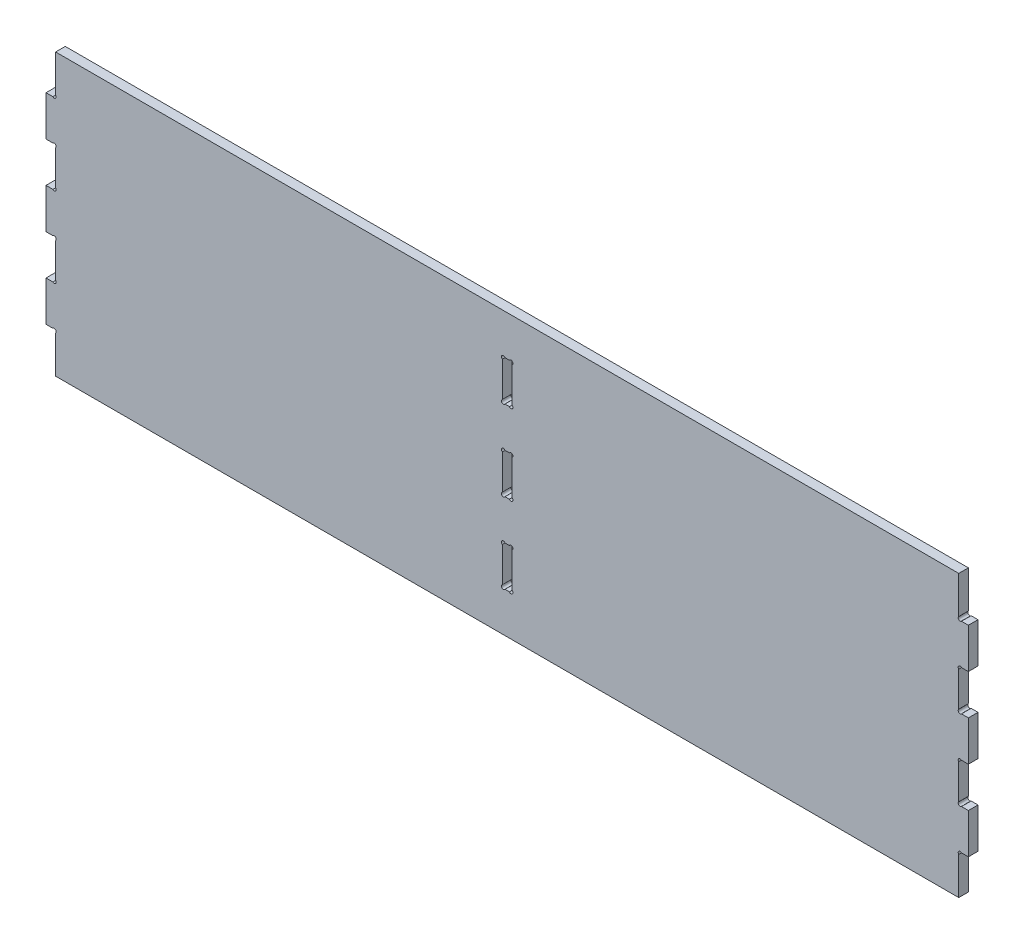
SolidWorks part; units mm, degrees
ref_plane "Front Plane" through (0, 0, 0) normal (0, 0, 1) x (1, 0, 0)
ref_plane "Top Plane" through (0, 0, 0) normal (0, 1, 0) x (1, 0, 0)
ref_plane "Right Plane" through (0, 0, 0) normal (1, 0, 0) x (0, 0, -1)
sketch "Sketch1" plane through (0, 0, 0) normal (0, 0, 1) x (1, 0, 0)
  line L0 (511.8067, 188.9039) -> (511.8067, 142.2993)
  line L1 (-613.9221, 188.9039) -> (511.8067, 188.9039)
  line L2 (-625.9221, -111.0961) -> (-625.9221, -61.0961)
  line L3 (-613.9221, -161.0961) -> (511.8067, -161.0961)
  line L4 (523.8067, 138.3198) -> (523.8067, 88.9039)
  line L5 (512.303, 138.9063) -> (512.303, 88.9039) construction
  line L6 (518.8067, 88.9039) -> (515.202, 88.9039)
  line L7 (511.8067, 85.5109) -> (511.8067, 42.2969)
  line L8 (515.202, 38.9039) -> (518.8067, 38.9039)
  line L9 (523.8067, 38.9039) -> (523.8067, -11.0961)
  line L10 (518.8067, -11.0961) -> (515.202, -11.0961)
  line L11 (511.8067, -14.4891) -> (511.8067, -57.7031)
  line L12 (515.202, -61.0961) -> (518.8067, -61.0961)
  line L13 (523.8067, -61.0961) -> (523.8067, -111.0961)
  line L14 (518.8067, -111.0961) -> (515.202, -111.0961)
  line L15 (511.8067, -114.4891) -> (511.8067, -161.0961)
  line L16 (523.8067, 138.3198) -> (523.8067, 138.9063)
  line L17 (523.8067, 88.9039) -> (518.8067, 88.9039)
  line L18 (518.8067, 38.9039) -> (523.8067, 38.9039)
  line L19 (523.8067, -11.0961) -> (518.8067, -11.0961)
  line L20 (518.8067, -61.0961) -> (523.8067, -61.0961)
  line L21 (523.8067, -111.0961) -> (518.8067, -111.0961)
  line L22 (-625.9221, 88.9039) -> (-625.9221, 138.3198)
  line L23 (523.8067, -98.3448) -> (-625.9221, -98.3448) construction
  line L24 (523.8067, 138.9063) -> (515.202, 138.9063)
  line L25 (512.303, 113.9051) -> (524.4814, 113.9051) construction
  line L26 (512.303, 141.3063) -> (512.303, 140.6015) construction
  line L27 (512.303, 140.6015) -> (513.9987, 140.6015) construction
  line L28 (512.303, 138.9063) -> (514.703, 138.9063) construction
  line L29 (514.703, 138.9063) -> (513.503, 138.9063) construction
  line L30 (513.503, 138.9063) -> (513.503, 140.6015) construction
  line L31 (-625.9221, 138.3198) -> (-625.9221, 138.9063)
  line L32 (512.303, 88.9039) -> (512.303, 38.9039) construction
  line L33 (512.303, 63.9039) -> (525.303, 63.9039) construction
  line L34 (512.303, 38.9039) -> (512.303, -11.0961) construction
  line L35 (512.303, 13.9039) -> (527.9398, 13.9039) construction
  line L36 (512.303, -11.0961) -> (512.303, -61.0961) construction
  line L37 (512.303, -36.0961) -> (527.9398, -36.0961) construction
  line L38 (512.303, -61.0961) -> (512.303, -111.0961) construction
  line L39 (512.303, -86.0961) -> (525.303, -86.0961) construction
  line L40 (-51.0577, -161.0961) -> (-51.0577, 188.9039) construction
  line L41 (-613.9221, -114.4891) -> (-613.9221, -161.0961)
  line L42 (-48.3362, 138.9063) -> (-53.7793, 138.9063)
  line L43 (-625.9221, -111.0961) -> (-620.9221, -111.0961)
  line L44 (-620.9221, -111.0961) -> (-617.3174, -111.0961)
  line L45 (-620.9221, -61.0961) -> (-625.9221, -61.0961)
  line L46 (-617.3174, -61.0961) -> (-620.9221, -61.0961)
  line L47 (-613.9221, -14.4891) -> (-613.9221, -57.7031)
  line L48 (-625.9221, -11.0961) -> (-620.9221, -11.0961)
  line L49 (-620.9221, -11.0961) -> (-617.3174, -11.0961)
  line L50 (-620.9221, 38.9039) -> (-625.9221, 38.9039)
  line L51 (-617.3174, 38.9039) -> (-620.9221, 38.9039)
  line L52 (-613.9221, 85.5109) -> (-613.9221, 42.2969)
  line L53 (-620.9221, 88.9039) -> (-617.3174, 88.9039)
  line L54 (-625.9221, 88.9039) -> (-620.9221, 88.9039)
  line L55 (-625.9221, 138.9063) -> (-617.3174, 138.9063)
  line L56 (-619.3744, 138.9063) -> (-47.4577, 138.9063) construction
  line L57 (-613.9221, 188.9039) -> (-613.9221, 142.2993)
  line L58 (-625.9221, -11.0961) -> (-625.9221, 38.9039)
  line L59 (-45.0577, 138.9063) -> (219.8393, 138.9063) construction
  line L60 (-48.3362, 88.9063) -> (-53.7793, 88.9063)
  line L61 (-57.0577, 135.6279) -> (-57.0577, 92.1848)
  line L62 (-623.4221, 38.9039) -> (236.8492, 38.9039) construction
  line L63 (-619.1198, -61.0961) -> (273.345, -61.0961) construction
  line L64 (-45.0577, 138.9063) -> (-47.4577, 138.9063) construction
  line L65 (-48.3454, 38.9039) -> (-53.7701, 38.9039)
  line L66 (-52.2709, 38.9039) -> (-52.2709, -11.0961) construction
  line L67 (-48.3454, -11.0961) -> (-53.7701, -11.0961)
  line L68 (-57.0577, 35.6415) -> (-57.0577, -7.8337)
  line L69 (-48.3362, -61.0961) -> (-53.7793, -61.0961)
  line L70 (-52.2709, -61.0961) -> (-52.2709, -111.0961) construction
  line L71 (-48.3362, -111.0961) -> (-53.7793, -111.0961)
  line L72 (-57.0577, -64.3746) -> (-57.0577, -107.8177)
  line L73 (-47.4577, 138.9063) -> (-46.2577, 138.9063) construction
  line L74 (-46.2577, 138.9063) -> (-46.2577, 137.1356) construction
  line L75 (-45.0577, 136.5063) -> (-45.0577, 138.9063) construction
  line L76 (-45.0577, 137.7063) -> (-46.7388, 137.7063) construction
  line L77 (-45.0577, 135.6279) -> (-45.0577, 92.1848)
  line L78 (-52.2709, 138.9063) -> (-52.2709, 88.9063) construction
  line L79 (-52.2709, 88.9063) -> (-52.2709, 113.9063) construction
  line L80 (-52.2709, 113.9063) -> (-62.1489, 113.9063) construction
  line L81 (-45.0577, 38.9039) -> (-47.4577, 38.9039) construction
  line L82 (-47.4577, 38.9039) -> (-46.2577, 38.9039) construction
  line L83 (-46.2577, 38.9039) -> (-46.2577, 37.381) construction
  line L84 (-45.0577, 38.9039) -> (-45.0577, 36.536) construction
  line L85 (-45.0577, 36.536) -> (-45.0577, 37.72) construction
  line L86 (-45.0577, 37.72) -> (-46.7388, 37.72) construction
  line L87 (-45.0577, 35.6415) -> (-45.0577, -7.8337)
  line L88 (-52.2709, -11.0961) -> (-52.2709, 13.9039) construction
  line L89 (-52.2709, 13.9039) -> (-65.3111, 13.9039) construction
  line L90 (-45.0577, -61.0961) -> (-47.4577, -61.0961) construction
  line L91 (-47.4577, -61.0961) -> (-46.2577, -61.0961) construction
  line L92 (-46.2577, -61.0961) -> (-46.2577, -62.6126) construction
  line L93 (-45.0577, -61.0961) -> (-45.0577, -63.4961) construction
  line L94 (-45.0577, -63.4961) -> (-45.0577, -62.2961) construction
  line L95 (-45.0577, -62.2961) -> (-46.7388, -62.2961) construction
  line L96 (-45.0577, -64.3746) -> (-45.0577, -107.8177)
  line L97 (-52.2709, -111.0961) -> (-52.2709, -86.0961) construction
  line L98 (-52.2709, -86.0961) -> (-68.2582, -86.0961) construction
  circle A0 centre (512.303, 138.9063) radius 2.4 construction
  arc A1 (511.8067, 142.2993) -> (515.202, 138.9063) centre (513.503, 140.6015) ccw
  arc A2 (511.8067, 85.5109) -> (515.202, 88.9039) centre (513.503, 87.2087) cw
  arc A3 (511.8067, 42.2969) -> (515.202, 38.9039) centre (513.503, 40.599) ccw
  arc A4 (511.8067, -14.4891) -> (515.202, -11.0961) centre (513.503, -12.7913) cw
  arc A5 (511.8067, -57.7031) -> (515.202, -61.0961) centre (513.503, -59.401) ccw
  arc A6 (511.8067, -114.4891) -> (515.202, -111.0961) centre (513.503, -112.7913) cw
  arc A7 (-613.9221, -114.4891) -> (-617.3174, -111.0961) centre (-615.6184, -112.7913) ccw
  arc A8 (-613.9221, -57.7031) -> (-617.3174, -61.0961) centre (-615.6184, -59.401) cw
  arc A9 (-613.9221, -14.4891) -> (-617.3174, -11.0961) centre (-615.6184, -12.7913) ccw
  arc A10 (-613.9221, 42.2969) -> (-617.3174, 38.9039) centre (-615.6184, 40.599) cw
  arc A11 (-613.9221, 85.5109) -> (-617.3174, 88.9039) centre (-615.6184, 87.2087) ccw
  arc A12 (-613.9221, 142.2993) -> (-617.3174, 138.9063) centre (-615.6184, 140.6015) cw
  circle A13 centre (-45.0577, 138.9063) radius 2.4 construction
  arc A14 (-45.0577, 135.6279) -> (-48.3362, 138.9063) centre (-46.2577, 137.7063) ccw
  arc A15 (-57.0577, 135.6279) -> (-53.7793, 138.9063) centre (-55.8577, 137.7063) cw
  arc A16 (-57.0577, 92.1848) -> (-53.7793, 88.9063) centre (-55.8577, 90.1063) ccw
  arc A17 (-45.0577, 92.1848) -> (-48.3362, 88.9063) centre (-46.2577, 90.1063) cw
  circle A18 centre (-45.0577, 38.9039) radius 2.4 construction
  arc A19 (-45.0577, 35.6415) -> (-48.3454, 38.9039) centre (-46.2577, 37.72) ccw
  arc A20 (-57.0577, 35.6415) -> (-53.7701, 38.9039) centre (-55.8577, 37.72) cw
  arc A21 (-57.0577, -7.8337) -> (-53.7701, -11.0961) centre (-55.8577, -9.9122) ccw
  arc A22 (-45.0577, -7.8337) -> (-48.3454, -11.0961) centre (-46.2577, -9.9122) cw
  circle A23 centre (-45.0577, -61.0961) radius 2.4 construction
  arc A24 (-45.0577, -64.3746) -> (-48.3362, -61.0961) centre (-46.2577, -62.2961) ccw
  arc A25 (-57.0577, -64.3746) -> (-53.7793, -61.0961) centre (-55.8577, -62.2961) cw
  arc A26 (-57.0577, -107.8177) -> (-53.7793, -111.0961) centre (-55.8577, -109.8961) ccw
  arc A27 (-45.0577, -107.8177) -> (-48.3362, -111.0961) centre (-46.2577, -109.8961) cw
  point P3 (523.8067, 88.9039)
  point P7 (530.298, 138.4807)
  point P8 (523.8067, -11.0961)
  point P10 (523.8067, 38.9039)
  point P12 (523.8067, -111.0961)
  point P14 (523.8067, -61.0961)
  dimension "D11" = 4.8
  dimension "D13" = 4.8
  dimension "D15" = 4.8
  dimension "D17" = 6
  dimension "D27" = 4.8
  dimension "D28" = 4.8
  dimension "D19" = 4.8
  dimension "D21" = 4.8
  dimension "D22" = 4.8
  dimension "D3" = 18
  dimension "D4" = 50
  dimension "D5" = 50
  dimension "D6" = 50
  dimension "D7" = 50
  dimension "D8" = 50
  dimension "D9" = 50
  dimension "D10" = 0
  dimension "D12" = 5
  dimension "D14" = 5
  dimension "D16" = 5
  dimension "D18" = 5
  dimension "D20" = 5
  dimension "D23" = 6
  dimension "D26" = 6
  dimension "D31" = 12
extrude "Boss-Extrude1" add sketch "Sketch1" along normal blind 12
